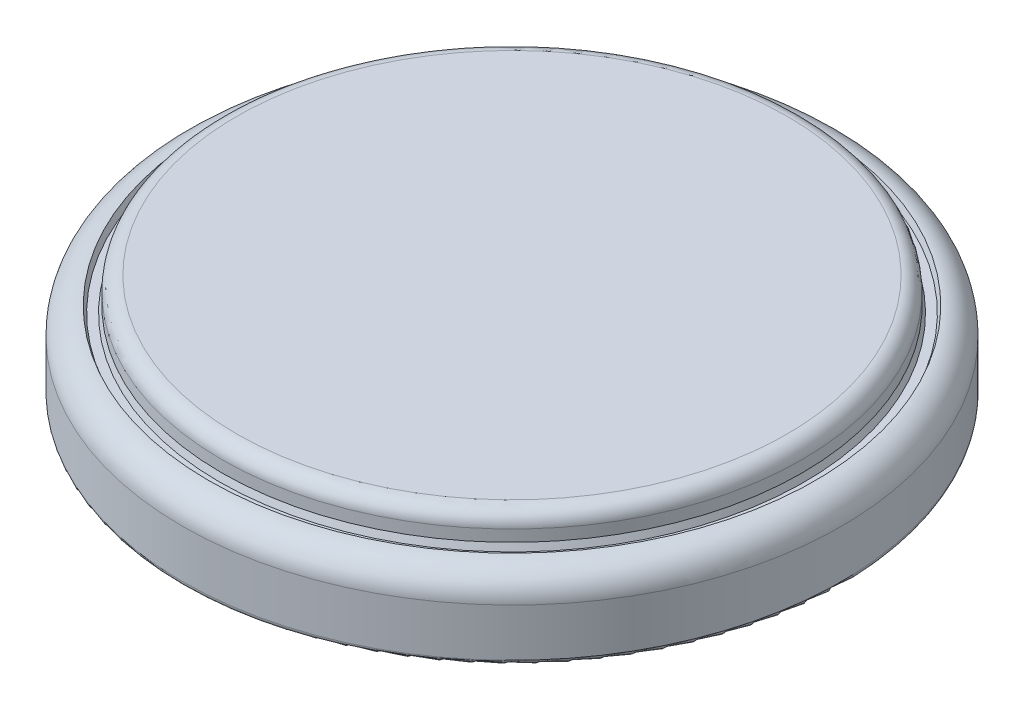
SolidWorks part; units mm, degrees
ref_plane "Front Plane" through (0, 0, 0) normal (0, 0, 1) x (1, 0, 0)
ref_plane "Top Plane" through (0, 0, 0) normal (0, 1, 0) x (1, 0, 0)
ref_plane "Right Plane" through (0, 0, 0) normal (1, 0, 0) x (0, 0, -1)
sketch "Sketch1" plane through (0, 0, 0) normal (0, 1, 0) x (1, 0, 0)
  circle A0 centre (0, 0) radius 10
  dimension "D1" = 20
extrude "Extrude1" add sketch "Sketch1" along normal blind 2.4
sketch "Sketch2" plane through (0, 0, 0) normal (0, 1, 0) x (1, 0, 0)
  circle A0 centre (0, 0) radius 8.8
  dimension "D1" = 17.6
extrude "Extrude2" add sketch "Sketch2" along normal blind 3.2
fillet "Fillet1" radius 0.8 1 edges at (0, 2.4, 10)
fillet "Fillet2" radius 0.15 1 edges at (0, 0, 10)
fillet "Fillet3" radius 0.45 1 edges at (0, 3.2, 8.8)
sketch "Sketch3" plane through (0, 2.4, 0) normal (0, 1, 0) x (-1, 0, 0)
  circle A0 centre (0, 0) radius 8.8 construction
  circle A1 centre (0, 0) radius 9.2
  circle A2 centre (0, 0) radius 9.2
  circle A3 centre (0, 0) radius 8.8
  dimension "D1" = 0
extrude "Cut-Extrude2" cut sketch "Sketch3" against normal blind 0.2 draft 20
sketch "Component_Outline" plane through (0, 0, 0) normal (0, 1, 0) x (1, 0, 0)
  circle A0 centre (0, 0) radius 10
  circle A1 centre (0, 0) radius 10 construction
